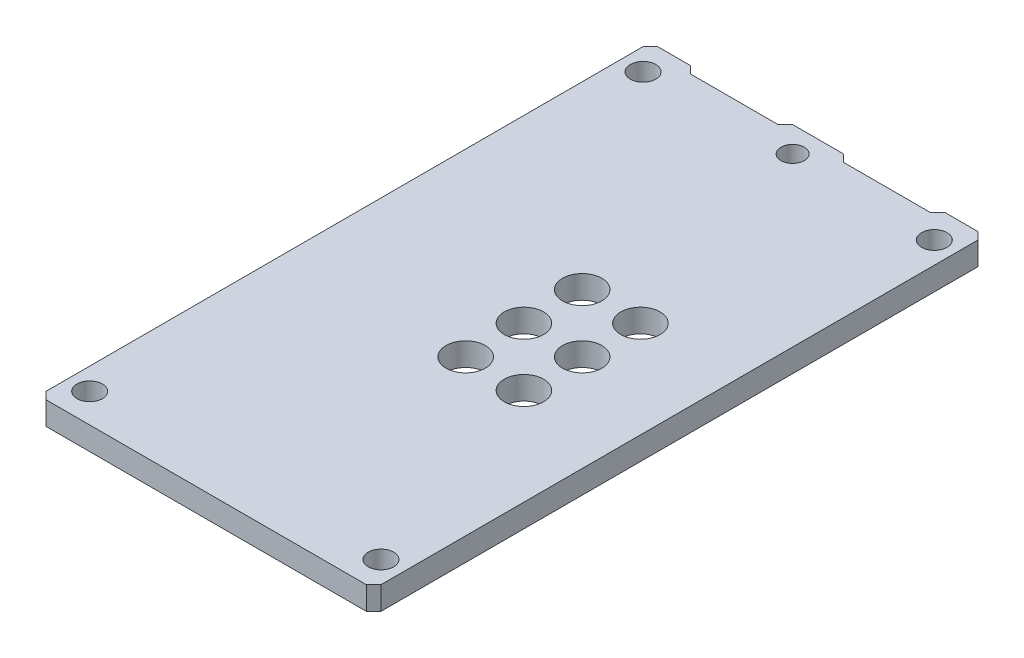
SolidWorks part; units mm, degrees
ref_plane "Front Plane" through (0, 0, 0) normal (0, 0, 1) x (1, 0, 0)
ref_plane "Top Plane" through (0, 0, 0) normal (0, 1, 0) x (1, 0, 0)
ref_plane "Right Plane" through (0, 0, 0) normal (1, 0, 0) x (0, 0, -1)
sketch "Sketch1" plane through (0, 0, 0) normal (0, 1, 0) x (1, 0, 0)
  line L0 (22.5, 0) -> (23, 0.5)
  line L1 (0, 0) -> (23, 0) construction
  line L2 (0, 0) -> (0, 42) construction
  line L3 (0, 42) -> (23, 42) construction
  line L4 (23, 0) -> (23, 42) construction
  line L5 (23, 0.5) -> (23, 41.5)
  line L6 (23, 41.5) -> (22.5, 42)
  line L7 (9.75, 42) -> (13.25, 42)
  line L8 (9.75, 42) -> (9.25, 41.5)
  line L9 (9.25, 41.5) -> (3.25, 41.5)
  line L10 (3.25, 41.5) -> (2.75, 42)
  line L11 (2.75, 42) -> (0.5, 42)
  line L12 (0.5, 42) -> (0, 41.5)
  line L13 (0, 41.5) -> (0, 0.5)
  line L14 (0, 0.5) -> (0.5, 0)
  line L15 (0.5, 0) -> (22.5, 0)
  line L16 (0, 41.5) -> (23, 41.5) construction
  line L17 (0, 0.5) -> (23, 0.5) construction
  line L18 (6.8436, 0.5) -> (6.8436, 0) construction
  line L19 (8.8632, 41.5) -> (8.8632, 42) construction
  line L20 (13.25, 42) -> (13.75, 41.5)
  line L21 (13.75, 41.5) -> (19.75, 41.5)
  line L22 (19.75, 41.5) -> (20.25, 42)
  line L23 (20.25, 42) -> (22.5, 42)
  line L24 (0, 40) -> (23, 40) construction
  line L25 (23, 2) -> (0, 2) construction
  line L26 (1.5, 42) -> (1.5, 0) construction
  line L27 (21.5, 42.6101) -> (21.5, 0) construction
  circle A0 centre (8.36, 16.96) radius 1.35 construction
  circle A1 centre (12.36, 16.96) radius 1.35
  circle A2 centre (16.36, 16.96) radius 1.35
  circle A3 centre (8.36, 20.96) radius 1.35 construction
  circle A4 centre (12.36, 20.96) radius 1.35
  circle A5 centre (16.36, 20.96) radius 1.35
  circle A6 centre (8.36, 24.96) radius 1.35 construction
  circle A7 centre (12.36, 24.96) radius 1.35
  circle A8 centre (16.36, 24.96) radius 1.35
  circle A9 centre (21.5, 40) radius 0.875
  circle A10 centre (21.5, 2) radius 0.875
  circle A11 centre (1.5, 2) radius 0.875
  circle A12 centre (1.5, 40) radius 0.875
  circle A13 centre (11.5154, 40.2552) radius 0.8001
  dimension "D1" = 3
  dimension "D2" = 3
extrude "Boss-Extrude1" add sketch "Sketch1" along normal blind 1.5875
